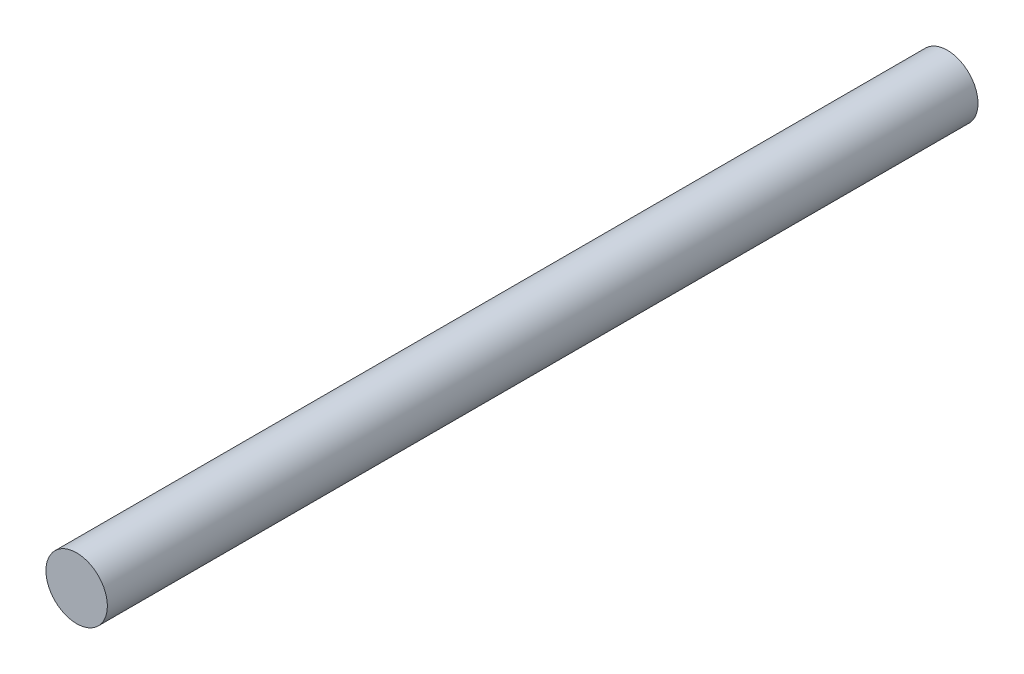
SolidWorks part; units mm, degrees
ref_plane "Alzado" through (0, 0, 0) normal (0, 0, 1) x (1, 0, 0)
ref_plane "Planta" through (0, 0, 0) normal (0, 1, 0) x (1, 0, 0)
ref_plane "Vista lateral" through (0, 0, 0) normal (1, 0, 0) x (0, 0, -1)
sketch "Croquis1" plane through (0, 0, 0) normal (0, 0, 1) x (1, 0, 0)
  circle A0 centre (0, 0) radius 6.35
  dimension "D1" = 12.7
sketch "Croquis2" plane through (0, 0, 0) normal (1, 0, 0) x (0, 0, -1)
  line L0 (0, 0) -> (180, 0)
  dimension "D1" = 180
sweep "Barrer1" add profiles "Croquis1" path "Croquis2"
